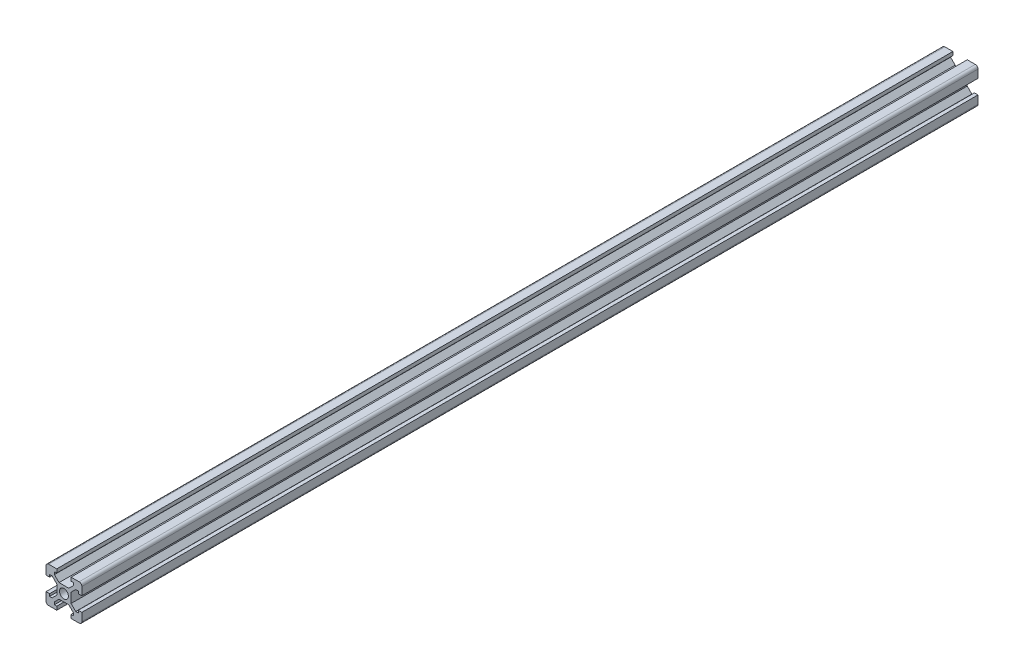
SolidWorks part; units mm, degrees
material "1060 Сплав"
ref_plane "Top" through (0, 0, 0) normal (0, 0, 1) x (1, 0, 0)
ref_plane "Сверху" through (0, 0, 0) normal (0, 1, 0) x (1, 0, 0)
ref_plane "Справа" through (0, 0, 0) normal (1, 0, 0) x (0, 0, -1)
sketch "Эскиз1" plane through (0, 0, 0) normal (0, 0, 1) x (1, 0, 0)
  line L0 (14, 20) -> (20, 20)
  line L1 (0, 0) -> (6, 0)
  line L2 (0, 0) -> (0, 6)
  line L3 (0, 20) -> (6, 20)
  line L4 (20, 0) -> (20, 6)
  line L5 (0, 14) -> (0, 20)
  line L6 (14, 0) -> (20, 0)
  line L7 (20, 14) -> (20, 20)
  line L8 (0, 0) -> (35355.3391, 35355.3391) construction
  line L9 (0, 20) -> (35355.3391, -35335.3391) construction
  line L22 (0, 14) -> (2, 14)
  line L23 (2, 14) -> (2, 15.3)
  line L24 (2, 15.3) -> (3.4272, 15.3)
  line L25 (3.4272, 15.3) -> (6, 12.7272)
  line L26 (6, 12.7272) -> (6, 7.2728)
  line L27 (6, 7.2728) -> (3.4272, 4.7)
  line L28 (3.4272, 4.7) -> (2, 4.7)
  line L29 (2, 4.7) -> (2, 6)
  line L30 (2, 6) -> (0, 6)
  line L31 (6, 0) -> (6, 2)
  line L32 (6, 2) -> (4.7, 2)
  line L33 (4.7, 2) -> (4.7, 3.4272)
  line L34 (4.7, 3.4272) -> (7.2728, 6)
  line L35 (7.2728, 6) -> (12.684, 6)
  line L36 (12.684, 6) -> (15.3, 3.4272)
  line L37 (15.3, 3.4272) -> (15.3, 2)
  line L38 (15.3, 2) -> (14, 2)
  line L39 (14, 2) -> (14, 0)
  line L40 (20, 6) -> (18, 6)
  line L41 (18, 6) -> (18, 4.7)
  line L42 (18, 4.7) -> (16.5728, 4.7)
  line L43 (16.5728, 4.7) -> (14, 7.2728)
  line L44 (14, 7.2728) -> (14, 12.7272)
  line L45 (14, 12.7272) -> (16.5728, 15.3)
  line L46 (16.5728, 15.3) -> (18, 15.3)
  line L47 (18, 15.3) -> (18, 14)
  line L48 (18, 14) -> (20, 14)
  line L49 (6, 20) -> (6, 18)
  line L50 (6, 18) -> (4.7, 18)
  line L51 (4.7, 18) -> (4.7, 16.5728)
  line L52 (4.7, 16.5728) -> (7.2728, 14)
  line L53 (7.2728, 14) -> (12.7272, 14)
  line L54 (12.7272, 14) -> (15.3, 16.5728)
  line L55 (15.3, 16.5728) -> (15.3, 18)
  line L56 (15.3, 18) -> (14, 18)
  line L57 (14, 18) -> (14, 20)
  circle A0 centre (10, 10) radius 2.5
extrude "Бобышка-Вытянуть1" add sketch "Эскиз1" along normal blind 500
fillet "Скругление1" radius 1.5 4 edges at (0, 20, 250) (20, 20, 250) (20, 0, 250) (0, 0, 250)
